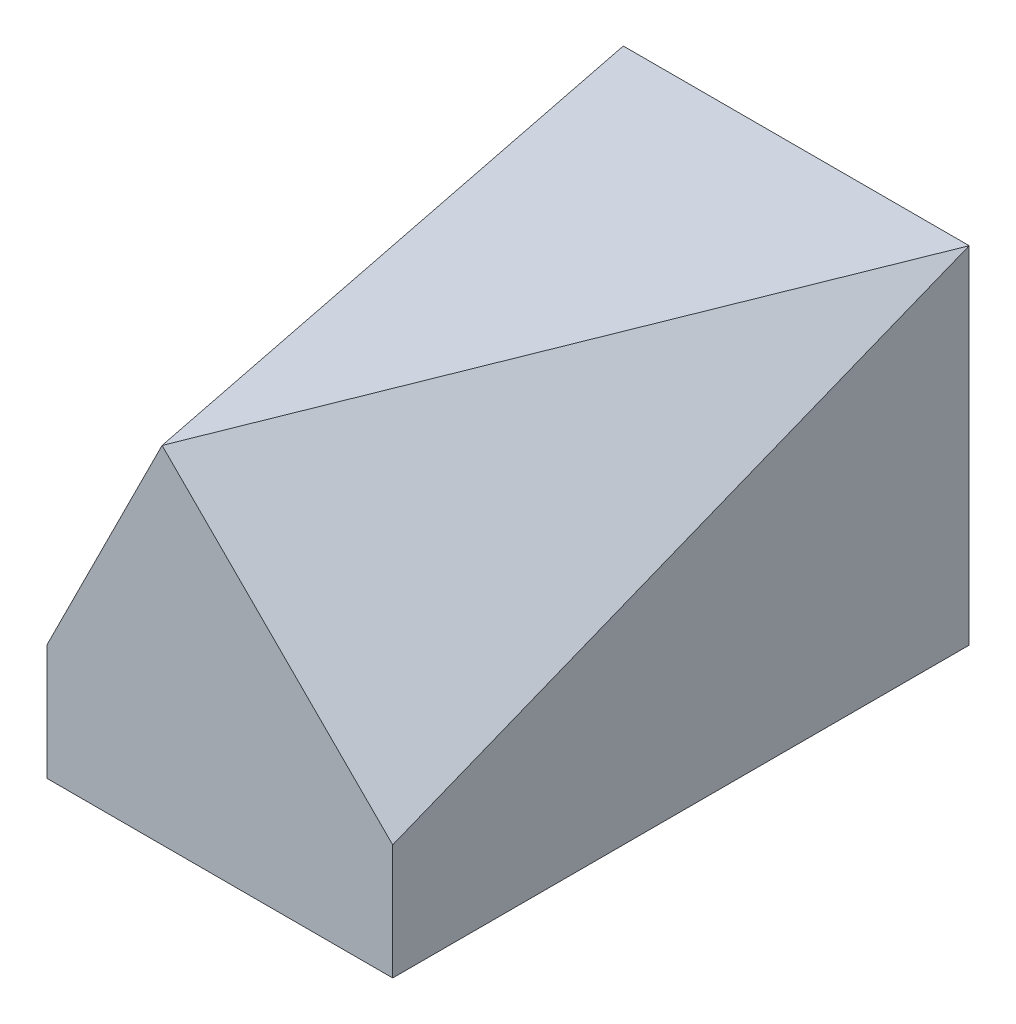
SolidWorks part; units mm, degrees
ref_plane "前基準面" through (0, 0, 0) normal (0, 0, 1) x (1, 0, 0)
ref_plane "上基準面" through (0, 0, 0) normal (0, 1, 0) x (1, 0, 0)
ref_plane "右基準面" through (0, 0, 0) normal (1, 0, 0) x (0, 0, -1)
sketch "草圖1" plane through (0, 0, 0) normal (0, 1, 0) x (1, 0, 0)
  line L1 (-7.5, -12.5) -> (7.5, -12.5)
  line L2 (-7.5, -12.5) -> (-7.5, 12.5)
  line L3 (-7.5, 12.5) -> (7.5, 12.5)
  line L4 (7.5, -12.5) -> (7.5, 12.5)
  line L5 (-7.5, -12.5) -> (7.5, 12.5) construction
  line L6 (-7.5, 12.5) -> (7.5, -12.5) construction
  point P0 (0, 0)
  dimension "D1" = 25
  dimension "D2" = 15
extrude "填料-伸長1" add sketch "草圖1" along normal blind 15
sketch "草圖2" plane through (0, 0, 12.5) normal (0, 0, 1) x (1, 0, 0)
  line L0 (-2.5, 15) -> (-7.5, 5)
  line L1 (-7.5, 15) -> (7.5, 15) construction
  line L2 (-7.5, 15) -> (-7.5, 0) construction
  line L3 (-2.5, 15) -> (7.5, 5)
  line L4 (7.5, 15) -> (7.5, 0) construction
  dimension "D1" = 10
  dimension "D2" = 5
sketch "草圖3" plane through (0, 15, 0) normal (0, 1, 0) x (1, 0, 0)
  line L0 (-2.5, -12.5) -> (-7.5, 12.5)
  line L1 (-2.5, -12.5) -> (7.5, -12.5) construction
  line L2 (-2.5, -12.5) -> (7.5, 12.5)
  line L3 (7.5, 12.5) -> (-7.5, 12.5) construction
  line L4 (7.5, -12.5) -> (7.5, 12.5) construction
  dimension "D1" = 5
ref_plane "平面1" through (-9.6899, 4.845, 1.938) normal (-0.8805, 0.4402, 0.1761) x (0.1575, -0.0787, 0.9844)
sketch "草圖4" plane through (-9.6899, 4.845, 1.938) normal (-0.8805, 0.4402, 0.1761) x (0.1575, -0.0787, 0.9844)
  line L1 (-15.1637, 18.6746) -> (18.2966, 18.6746)
  line L2 (-15.1637, 18.6746) -> (-15.1637, -8.0133)
  line L3 (-15.1637, -8.0133) -> (18.2966, -8.0133)
  line L4 (18.2966, 18.6746) -> (18.2966, -8.0133)
extrude "除料-伸長1" cut sketch "草圖4" along normal blind 15
ref_plane "平面2" through (8.1019, 8.1019, 3.2407) normal (-0.6804, -0.6804, -0.2722) x (-0.1925, -0.1925, 0.9623)
sketch "草圖5" plane through (8.1019, 8.1019, 3.2407) normal (-0.6804, -0.6804, -0.2722) x (-0.1925, -0.1925, 0.9623)
  line L1 (18.6645, 17.0838) -> (-22.3565, 17.0838)
  line L2 (18.6645, 17.0838) -> (18.6645, -6.1521)
  line L3 (18.6645, -6.1521) -> (-22.3565, -6.1521)
  line L4 (-22.3565, 17.0838) -> (-22.3565, -6.1521)
extrude "除料-伸長2" cut sketch "草圖5" against normal blind 15
